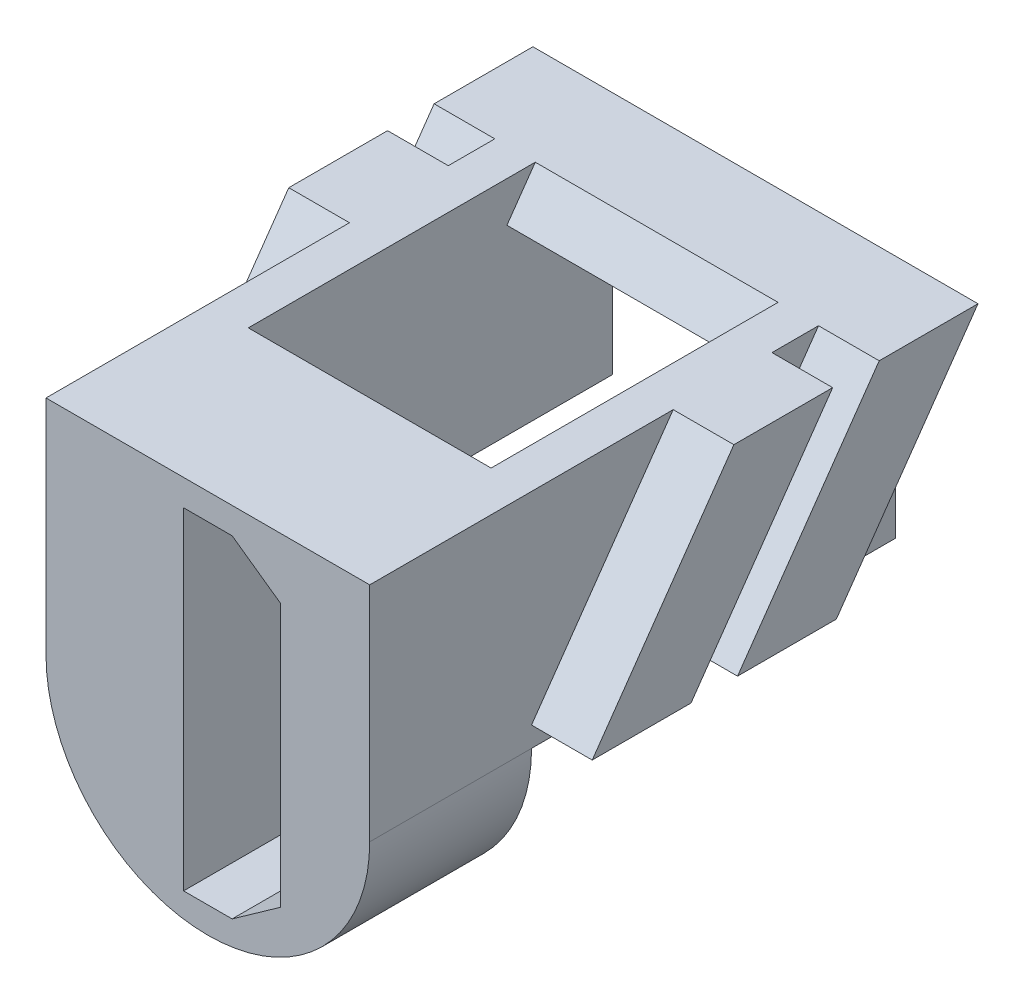
SolidWorks part; units mm, degrees
ref_plane "Front Plane" through (0, 0, 0) normal (0, 0, 1) x (1, 0, 0)
ref_plane "Top Plane" through (0, 0, 0) normal (0, 1, 0) x (1, 0, 0)
ref_plane "Right Plane" through (0, 0, 0) normal (1, 0, 0) x (0, 0, -1)
sketch "Sketch1" plane through (0, 0, 0) normal (0, 0, 1) x (1, 0, 0)
  line L0 (-4, -0.75) -> (-4, 4.75)
  line L1 (-4, 4.75) -> (4, 4.75)
  line L2 (4, 4.75) -> (4, -0.75)
  line L3 (0, 4.75) -> (0, 0) construction
  line L4 (0, 0) -> (0, -4.75) construction
  arc A0 (-4, -0.75) -> (4, -0.75) centre (0, -0.75) ccw
  dimension "D1" = 8
  dimension "D2" = 5.5
extrude "Boss-Extrude1" add sketch "Sketch1" along normal mid plane 13
sketch "Sketch2" plane through (0, 0, 0) normal (1, 0, 0) x (0, 0, -1)
  line L1 (-2.501, -0.25) -> (-0.0595, -0.25)
  line L6 (4.5915, 4.75) -> (4.0215, 3.9359)
  line L7 (1, 4.75) -> (-2.501, -0.25)
  line L8 (-6.5, 4.75) -> (6.5, 4.75) construction
  line L9 (2.3994, 3.2617) -> (3.4415, 4.75)
  line L11 (-0.0595, -0.25) -> (2.3994, 3.2617)
  line L12 (3.4415, 4.75) -> (1, 4.75)
  line L13 (1.0905, -0.25) -> (3.5321, -0.25)
  line L14 (3.5321, -0.25) -> (7.0331, 4.75)
  line L18 (4.5915, 4.75) -> (7.0331, 4.75)
  line L19 (4.0215, 3.9359) -> (3.6903, 3.4629)
  line L20 (3.6903, 3.4629) -> (1.0905, -0.25)
  dimension "D1" = 7.5
  dimension "D2" = 55
  dimension "D3" = 2
  dimension "D4" = 5
  dimension "D5" = 1.15
extrude "Boss-Extrude2" add sketch "Sketch2" along normal blind 5.5 and the other way blind 5.5
sketch "Sketch3" plane through (0, 0, 6.5) normal (0, 0, 1) x (1, 0, 0)
  line L3 (4, -0.75) -> (3, -0.75)
  line L4 (3, -0.75) -> (3, 4.75)
  line L5 (4, 4.75) -> (-4, 4.75) construction
  line L6 (3, 4.75) -> (-3, 4.75)
  line L7 (-3, 4.75) -> (-3, -0.75)
  line L8 (-3, -0.75) -> (-4, -0.75)
  arc A1 (-4, -0.75) -> (4, -0.75) centre (0, -0.75) ccw
  dimension "D1" = 1
extrude "Cut-Extrude1" cut sketch "Sketch3" against normal blind 25 from offset 4 offset against normal yes
sketch "Sketch4" plane through (0, 0, 0) normal (1, 0, 0) x (0, 0, -1)
  line L0 (7.0331, 4.75) -> (4.5915, 4.75)
  line L1 (4.5915, 4.75) -> (3.8913, 3.75)
  line L2 (1.0905, -0.25) -> (4.5915, 4.75) construction
  line L3 (3.8913, 3.75) -> (6.3329, 3.75)
  line L4 (3.5321, -0.25) -> (7.0331, 4.75) construction
  line L5 (6.3329, 3.75) -> (7.0331, 4.75)
  dimension "D1" = 1
extrude "Boss-Extrude3" add sketch "Sketch4" along normal up to surface and the other way up to surface up to face at (5.5, 2.25, -4.0618) other way up to face at (-5.5, 2.25, -4.0618)
sketch "Sketch5" plane through (0, 0, 6.5) normal (0, 0, 1) x (1, 0, 0)
  line L6 (-0.6, 4.1) -> (-0.6, -4.1)
  line L7 (-0.6, -4.1) -> (0.6, -4.1)
  line L8 (0.6, -4.1) -> (1.8, -3.25)
  line L9 (1.8, -3.25) -> (1.8, 3.25)
  line L10 (1.8, 3.25) -> (0.6, 4.1)
  line L11 (0.6, 4.1) -> (-0.6, 4.1)
  point P6 (-0.6, 0)
  point P7 (0, 4.1)
  dimension "D1" = 8.2
  dimension "D2" = 2.4
  dimension "D3" = 1.2
  dimension "D4" = 6.5
extrude "Cut-Extrude2" cut sketch "Sketch5" against normal up to surface (4 mm away) up to face at (0, 0.4167, 2.5)
fillet "Fillet2" [suppressed] radius 1
